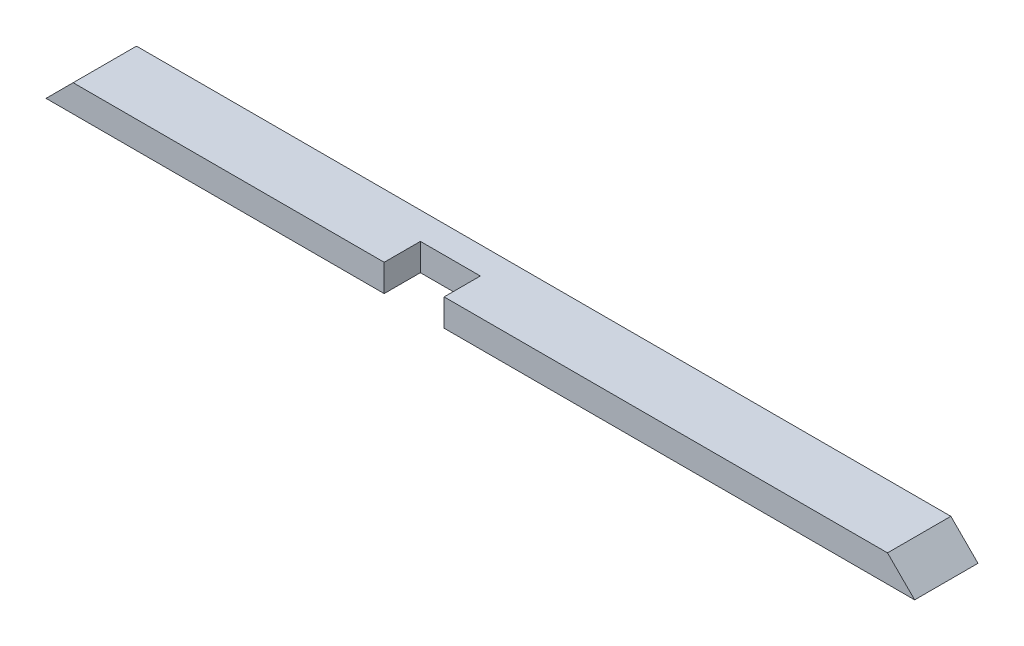
SolidWorks part; units mm, degrees
material "Pine"
ref_plane "Front Plane" through (0, 0, 0) normal (0, 0, 1) x (1, 0, 0)
ref_plane "Top Plane" through (0, 0, 0) normal (0, 1, 0) x (1, 0, 0)
ref_plane "Right Plane" through (0, 0, 0) normal (1, 0, 0) x (0, 0, -1)
sketch "Sketch1" plane through (0, 0, 0) normal (0, 1, 0) x (1, 0, 0)
  line L1 (0, 0) -> (1219.2, 0)
  line L2 (0, 0) -> (0, 88.9)
  line L3 (0, 88.9) -> (1219.2, 88.9)
  line L4 (1219.2, 0) -> (1219.2, 88.9)
  dimension "D1" = 88.9
  dimension "D2" = 1219.2
extrude "Boss-Extrude1" add sketch "Sketch1" along normal blind 38.1
sketch "Sketch2" plane through (0, 0, 0) normal (0, 0, 1) x (1, 0, 0)
  line L0 (0, 0) -> (38.1, 38.1)
  line L1 (0, 38.1) -> (1219.2, 38.1) construction
  line L2 (38.1, 38.1) -> (0, 38.1)
  line L3 (0, 38.1) -> (0, 0)
  line L5 (1219.2, 0) -> (1219.2, 38.1)
  line L9 (1219.2, 38.1) -> (1181.1, 38.1)
  line L10 (1181.1, 38.1) -> (1219.2, 0)
  dimension "D1" = 38.1
  dimension "D2" = 38.1
  dimension "D3" = 38.1
extrude "Cut-Extrude1" cut sketch "Sketch2" against normal through all
sketch "Sketch3" plane through (0, 0, 0) normal (0, -1, 0) x (1, 0, 0)
  line L0 (0, 0) -> (1219.2, 0) construction
  line L1 (558.8, 0) -> (474.6625, 0)
  line L2 (558.8, 0) -> (558.8, -50.8)
  line L3 (558.8, -50.8) -> (474.6625, -50.8)
  line L4 (474.6625, 0) -> (474.6625, -50.8)
  line L5 (0, -88.9) -> (0, 0) construction
  point P8 (474.6625, -25.4)
  dimension "D1" = 84.1375
  dimension "D2" = 50.8
  dimension "D3" = 474.6625
extrude "Cut-Extrude2" cut sketch "Sketch3" against normal through all
